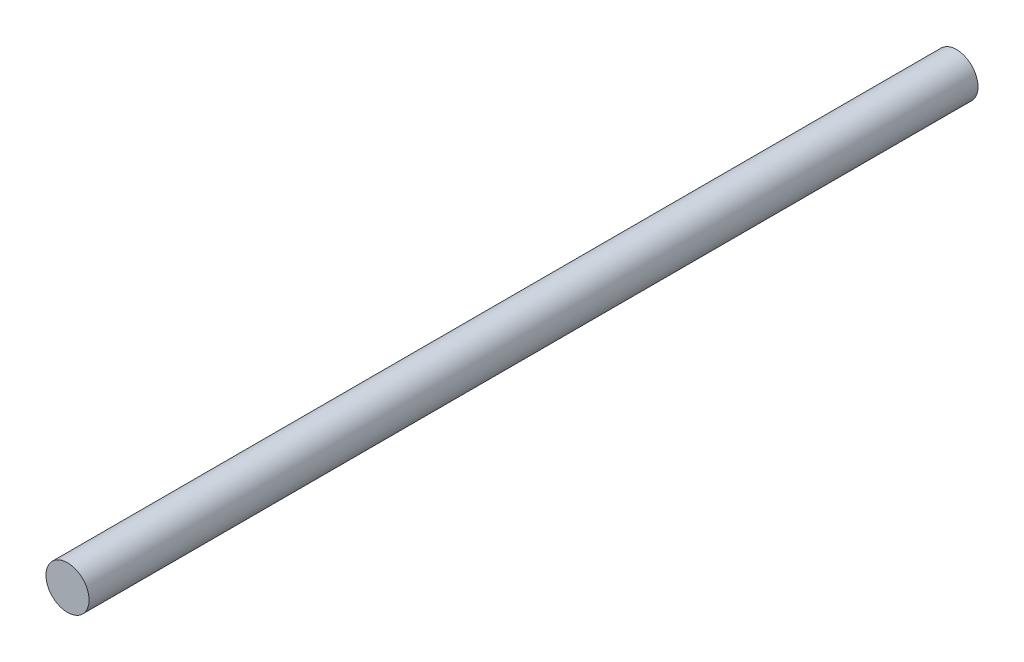
SolidWorks part; units mm, degrees
material "A286 铁基超合金"
ref_plane "前视基准面" through (0, 0, 0) normal (0, 0, 1) x (1, 0, 0)
ref_plane "上视基准面" through (0, 0, 0) normal (0, 1, 0) x (1, 0, 0)
ref_plane "右视基准面" through (0, 0, 0) normal (1, 0, 0) x (0, 0, -1)
sketch "草图3" plane through (0, 0, 0) normal (0, 0, 1) x (1, 0, 0)
  circle A0 centre (0, 0) radius 4
  dimension "D1" = 8
extrude "凸台-拉伸1" add sketch "草图3" along normal mid plane 165
